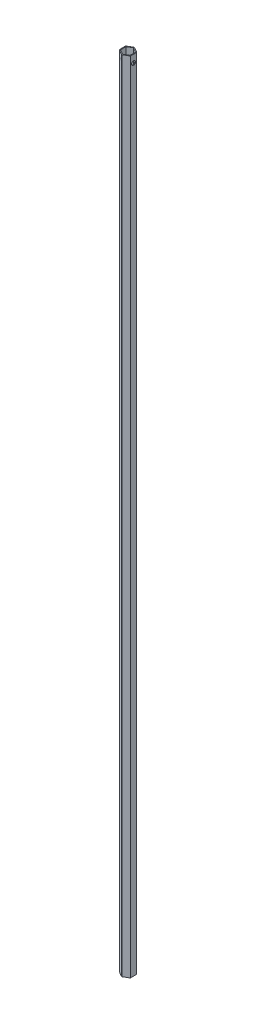
SolidWorks part; units mm, degrees
material "Default"
ref_plane "Front Plane" through (0, 0, 0) normal (0, 0, 1) x (1, 0, 0)
ref_plane "Top Plane" through (0, 0, 0) normal (0, 1, 0) x (1, 0, 0)
ref_plane "Right Plane" through (0, 0, 0) normal (1, 0, 0) x (0, 0, -1)
sketch "Sketch1" plane through (0, 0, 0) normal (0, 1, 0) x (1, 0, 0)
  line L13 (-9.2255, 5.2847) -> (-9.1894, -5.3471)
  line L14 (-9.1894, -5.3471) -> (0.036, -10.6318)
  line L15 (0.036, -10.6318) -> (9.2255, -5.2847)
  line L16 (9.2255, -5.2847) -> (9.1894, 5.3471)
  line L17 (9.1894, 5.3471) -> (-0.036, 10.6318)
  line L18 (-0.036, 10.6318) -> (-9.2255, 5.2847)
  line L19 (-7.983, 4.503) -> (-7.8912, -4.662)
  line L20 (-7.8912, -4.662) -> (0.0918, -9.165)
  line L21 (0.0918, -9.165) -> (7.983, -4.503)
  line L22 (7.983, -4.503) -> (7.8912, 4.662)
  line L23 (7.8912, 4.662) -> (-0.0918, 9.165)
  line L24 (-0.0918, 9.165) -> (-7.983, 4.503)
  circle A0 centre (0, 0) radius 9.2075 construction
  circle A1 centre (0, 0) radius 7.9375 construction
  point P0 (0, 0)
  point P6 (0, 0)
  dimension "D1" = 15.875
  dimension "D2" = 18.415
extrude "Boss-Extrude1" add sketch "Sketch1" along normal blind 1322.07
fillet "Fillet1" radius 1.27 6 edges at (9.1894, 661.035, -5.3471) (-0.036, 661.035, -10.6318) (-9.2255, 661.035, -5.2847) (-9.1894, 661.035, 5.3471) (0.036, 661.035, 10.6318) (7.983, 661.035, 4.503)
sketch "Sketch2" plane through (0.0864, 0, 10.6607) normal (-0.4971, 0, 0.8677) x (0.8677, 0, 0.4971)
  line L1 (-9.9567, 1312.9046) -> (-0.7913, 1312.9046)
  line L2 (-9.9567, 1312.9046) -> (-9.9567, 1322.07)
  line L3 (-9.9567, 1322.07) -> (-0.7913, 1322.07)
  line L4 (-0.7913, 1312.9046) -> (-0.7913, 1322.07)
  line L5 (-9.9567, 1312.9046) -> (-0.7913, 1322.07) construction
  line L6 (-9.9567, 1322.07) -> (-0.7913, 1312.9046) construction
  line L9 (-9.9567, 1322.07) -> (-9.9567, 0) construction
  line L10 (-0.7913, 0) -> (-0.7913, 1322.07) construction
  line L12 (-9.9567, 1322.07) -> (-0.7913, 1322.07) construction
  point P0 (-5.374, 1317.4873)
  point P5 (-7.6674, 9.0772)
  point P6 (-13.5424, 1.3325)
split line "Split Line1"
sketch "Sketch3" plane through (0, 0, 0) normal (0, -1, 0) x (1, 0, 0)
  line L6 (0.6002, -10.2674) -> (8.5532, -5.7116)
  line L7 (9.1919, -4.6139) -> (9.2255, 5.2847)
  line L12 (9.2255, 5.2847) -> (0.6698, 10.2631)
  line L13 (-0.6002, 10.2674) -> (-8.5532, 5.7116)
  line L14 (-9.1919, 4.6139) -> (-9.223, -4.5515)
  line L15 (-8.5917, -5.6535) -> (-0.6698, -10.2631)
  line L16 (0.6002, -10.2674) -> (8.5532, -5.7116)
  line L17 (9.1919, -4.6139) -> (9.2255, 5.2847)
  line L18 (9.2255, 5.2847) -> (0.6698, 10.2631)
  line L20 (-9.1919, 4.6139) -> (-9.223, -4.5515)
  line L21 (-8.5917, -5.6535) -> (-0.6698, -10.2631)
  line L22 (-0.6002, 10.2674) -> (-8.5532, 5.7116)
  arc A6 (8.5532, -5.7116) -> (9.1919, -4.6139) centre (7.9219, -4.6096) ccw
  arc A7 (0.6698, 10.2631) -> (-0.6002, 10.2674) centre (0.0311, 9.1654) ccw
  arc A12 (-8.5532, 5.7116) -> (-9.1919, 4.6139) centre (-7.9219, 4.6096) ccw
  arc A13 (-9.223, -4.5515) -> (-8.5917, -5.6535) centre (-7.953, -4.5558) ccw
  arc A14 (-0.6698, -10.2631) -> (0.6002, -10.2674) centre (-0.0311, -9.1654) ccw
  arc A15 (8.5532, -5.7116) -> (9.1919, -4.6139) centre (7.9219, -4.6096) ccw
  arc A16 (0.6698, 10.2631) -> (-0.6002, 10.2674) centre (0.0311, 9.1654) ccw
  arc A17 (-8.5532, 5.7116) -> (-9.1919, 4.6139) centre (-7.9219, 4.6096) ccw
  arc A18 (-9.223, -4.5515) -> (-8.5917, -5.6535) centre (-7.953, -4.5558) ccw
  arc A19 (-0.6698, -10.2631) -> (0.6002, -10.2674) centre (-0.0311, -9.1654) ccw
  dimension "D1" = 0
extrude "Boss-Extrude2" add sketch "Sketch3" along normal blind 2.54
hole_wizard "1/4 (0.25) Diameter Hole1" positions "Sketch4" profile "Sketch5" hole size "1/4" standard "ANSI Inch" end condition through all
sketch "Sketch4" plane through (0, -2.54, 0) normal (0, -1, 0) x (-1, 0, 0)
  point P0 (0, 0)
sketch "Sketch5" plane through (0, -2.54, 0) normal (1, 0, 0) x (0, 0, -1)
  line L0 (0, 0) -> (0, 1324.61)
  line L1 (0, 1324.61) -> (3.175, 1324.61)
  line L2 (3.175, 1324.61) -> (3.175, 0)
  line L5 (3.175, 0) -> (0, 0)
  line L11 (0, -6.35) -> (0, 107.95) construction
  dimension "Thru Hole Dia." = 6.35
  dimension "Thru Hole Depth" = 1324.61
hole_wizard "1/4 Clearance Hole1" positions "Sketch6" profile "Sketch7" hole size "1/4" standard "ANSI Inch" end condition through all
sketch "Sketch6" plane through (9.2076, 0, 0.003) normal (1, 0, -0.0034) x (-0.0034, 0, -1)
  line L1 (-5.2817, 1322.07) -> (4.6169, 1322.07) construction
  point P0 (0, 1309.37)
  dimension "D1" = 12.7
sketch "Sketch7" plane through (9.2076, 1309.37, 0.003) normal (0, 1, 0) x (-0.0034, 0, -1)
  line L0 (0, 0) -> (0, 18.4658)
  line L1 (0, 18.4658) -> (3.3782, 18.4658)
  line L2 (3.3782, 18.4658) -> (3.3782, 0)
  line L5 (3.3782, 0) -> (0, 0)
  line L11 (0, -6.35) -> (0, 107.95) construction
  dimension "Thru Hole Dia." = 6.7564
  dimension "Thru Hole Depth" = 18.4658
sketch "Sketch8" plane through (4.5767, 0, -7.9895) normal (-0.4971, 0, 0.8677) x (0.8677, 0, 0.4971)
  line L1 (-4.5827, 247.9254) -> (4.5827, 247.9254)
  line L2 (-4.5827, 247.9254) -> (-4.5827, 238.76)
  line L3 (-4.5827, 238.76) -> (4.5827, 238.76)
  line L4 (4.5827, 247.9254) -> (4.5827, 238.76)
  line L6 (-5.6826, -2.54) -> (-10.2653, -2.54) construction
  line L7 (-4.5827, -2.54) -> (-4.5827, 1322.07) construction
  line L8 (4.5827, 1322.07) -> (4.5827, -2.54) construction
  dimension "D1" = 241.3
split line "Split Line2"
